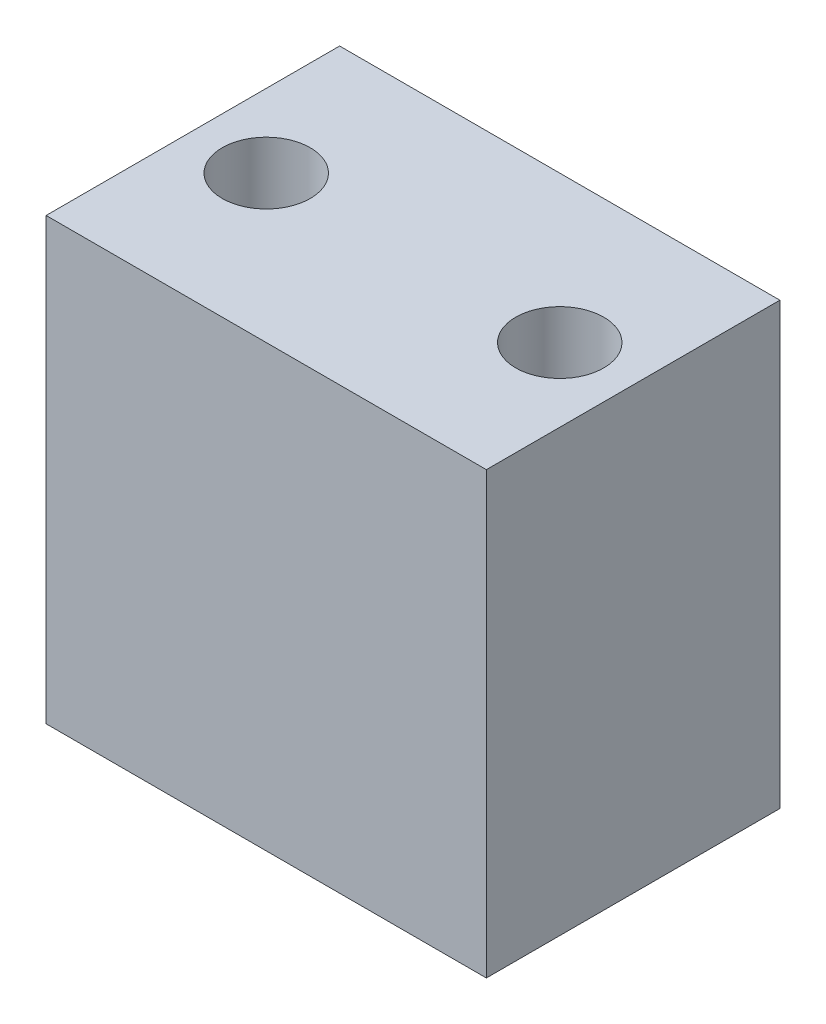
SolidWorks part; units mm, degrees
ref_plane "Front Plane" through (0, 0, 0) normal (0, 0, 1) x (1, 0, 0)
ref_plane "Top Plane" through (0, 0, 0) normal (0, 1, 0) x (1, 0, 0)
ref_plane "Right Plane" through (0, 0, 0) normal (1, 0, 0) x (0, 0, -1)
sketch "Sketch1" plane through (0, 0, 0) normal (0, 1, 0) x (1, 0, 0)
  line L1 (-38.1, 25.4) -> (0, 25.4)
  line L2 (-38.1, 25.4) -> (-38.1, 0)
  line L3 (-38.1, 0) -> (0, 0)
  line L4 (0, 25.4) -> (0, 0)
  circle A1 centre (-31.75, 12.7) radius 3.81
  circle A2 centre (-6.35, 12.7) radius 3.81
  dimension "D3" = 7.62
  dimension "D4" = 7.62
  dimension "D1" = 38.1
  dimension "D2" = 25.4
  dimension "D6" = 12.7
  dimension "D7" = 6.35
  dimension "D8" = 6.35
extrude "Boss-Extrude1" add sketch "Sketch1" along normal blind 38.1
